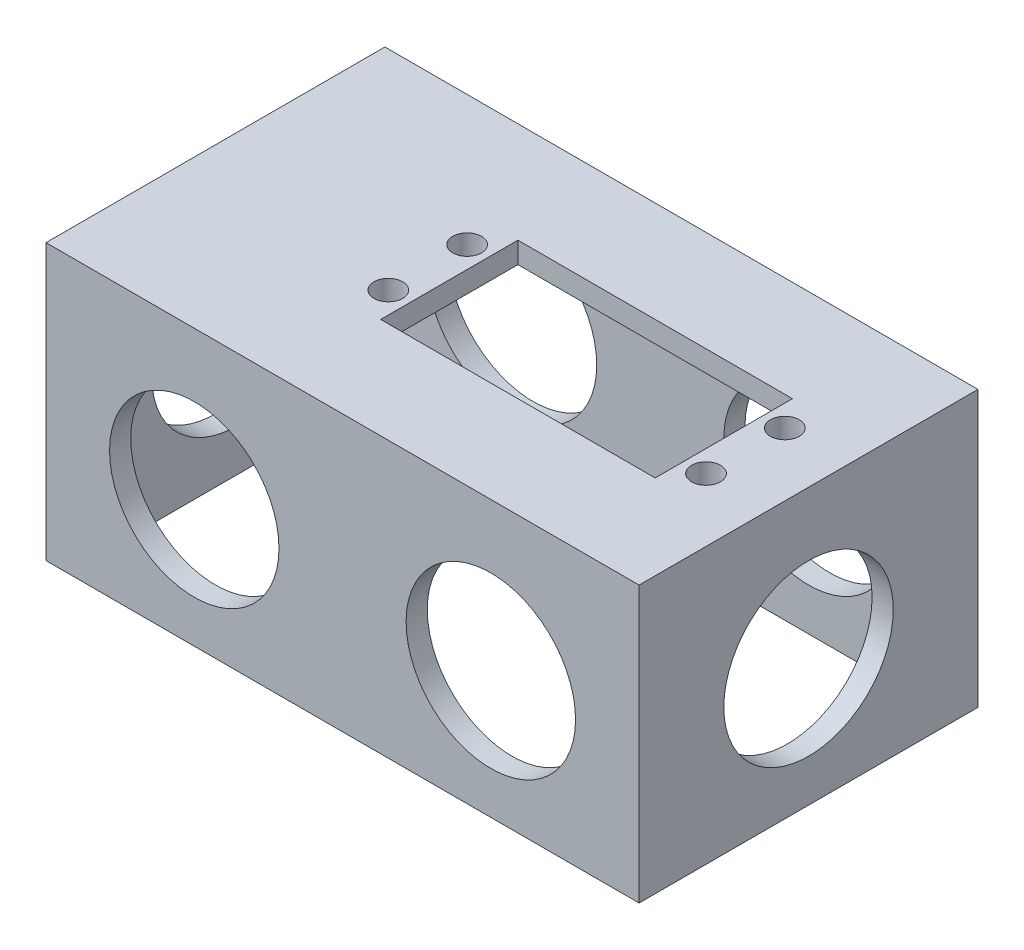
SolidWorks part; units mm, degrees
material "ABS"
ref_plane "Front" through (0, 0, 0) normal (0, 0, 1) x (1, 0, 0)
ref_plane "Top" through (0, 0, 0) normal (0, 1, 0) x (1, 0, 0)
ref_plane "Right" through (0, 0, 0) normal (1, 0, 0) x (0, 0, -1)
sketch "Sketch3" plane through (0, 0, 0) normal (0, 1, 0) x (1, 0, 0)
  line L0 (3.175, 3.175) -> (85.725, 3.175)
  line L1 (0, 0) -> (88.9, 0)
  line L2 (0, 0) -> (0, 50.8)
  line L3 (0, 50.8) -> (88.9, 50.8)
  line L4 (88.9, 0) -> (88.9, 50.8)
  line L5 (85.725, 3.175) -> (85.725, 47.625)
  line L6 (3.175, 47.625) -> (85.725, 47.625)
  line L7 (3.175, 3.175) -> (3.175, 47.625)
  dimension "D1" = 88.9
  dimension "D2" = 50.8
  dimension "D3" = 3.175
extrude "Boss-Extrude2" add sketch "Sketch3" along normal blind 38.1
sketch "Sketch4" plane through (88.9, 0, 0) normal (1, 0, 0) x (0, 0, -1)
  line L2 (0, 38.1) -> (50.8, 38.1) construction
  line L3 (25.4, 19.05) -> (25.4, 38.1) construction
  line L4 (25.4, 19.05) -> (50.8, 19.05) construction
  line L5 (50.8, 38.1) -> (50.8, 0) construction
  circle A0 centre (25.4, 19.05) radius 12.7
  dimension "D1" = 25.4
extrude "Cut-Extrude1" cut sketch "Sketch4" against normal up to surface (88.9 mm away) up to face at (0, 19.05, -25.4)
sketch "Sketch6" plane through (0, 38.1, 0) normal (0, 1, 0) x (1, 0, 0)
  line L1 (88.9, 50.8) -> (0, 50.8)
  line L2 (88.9, 50.8) -> (88.9, 0)
  line L3 (88.9, 0) -> (0, 0)
  line L4 (0, 50.8) -> (0, 0)
extrude "Boss-Extrude3" add sketch "Sketch6" along normal blind 3.175
sketch "Sketch7" plane through (0, 0, -50.8) normal (0, 0, -1) x (-1, 0, 0)
  line L0 (-44.45, 41.275) -> (-44.45, 0) construction
  line L1 (-88.9, 41.275) -> (0, 41.275) construction
  line L2 (-88.9, 0) -> (0, 0) construction
  line L3 (0, 19.05) -> (-76.2, 19.05) construction
  line L6 (-22.225, 19.05) -> (-22.225, 41.275) construction
  line L7 (-44.45, 41.275) -> (0, 41.275) construction
  line L8 (-88.9, 41.275) -> (-44.45, 41.275) construction
  line L9 (-66.675, 19.05) -> (-66.675, 41.275) construction
  circle A0 centre (-66.675, 19.05) radius 12.7
  circle A1 centre (-22.225, 19.05) radius 12.7
  point P19 (-22.225, 41.275)
  dimension "D1" = 25.4
  dimension "D2" = 19.05
extrude "Cut-Extrude2" cut sketch "Sketch7" against normal up to surface (50.8 mm away) up to face at (44.45, 20.6375, 0)
sketch "Sketch8" plane through (0, 41.275, 0) normal (0, 1, 0) x (1, 0, 0)
  line L0 (44.45, 0) -> (44.45, 50.8) construction
  line L1 (76.2, 15.113) -> (35.052, 15.113)
  line L2 (76.2, 15.113) -> (76.2, 35.687)
  line L3 (76.2, 35.687) -> (35.052, 35.687)
  line L4 (35.052, 15.113) -> (35.052, 35.687)
  line L5 (0, 0) -> (88.9, 0) construction
  line L6 (88.9, 50.8) -> (0, 50.8) construction
  point P10 (35.052, 25.4)
  point P11 (44.45, 25.4)
  point P12 (28.2575, 25.4)
  point P13 (55.626, 15.5575)
  point P14 (55.626, 15.113)
  line B0 (28.2575, 35.2425) -> (28.2575, 15.5575) construction
  line B1 (28.2575, 15.5575) -> (82.9945, 15.5575) construction
  circle B2 centre (31.8135, 31.3055) radius 2.159
  circle B3 centre (31.8135, 19.4945) radius 2.159
  circle B4 centre (79.4385, 19.4945) radius 2.159
  circle B5 centre (79.4385, 31.3055) radius 2.159
  dimension "D1" = 9.398
  dimension "D2" = 41.148
  dimension "D3" = 20.574
sketch_block_instance "ServoMountingHoles-1"
sketch_block "ServoMountingHoles"
extrude "Cut-Extrude3" cut sketch "Sketch8" against normal up to next
